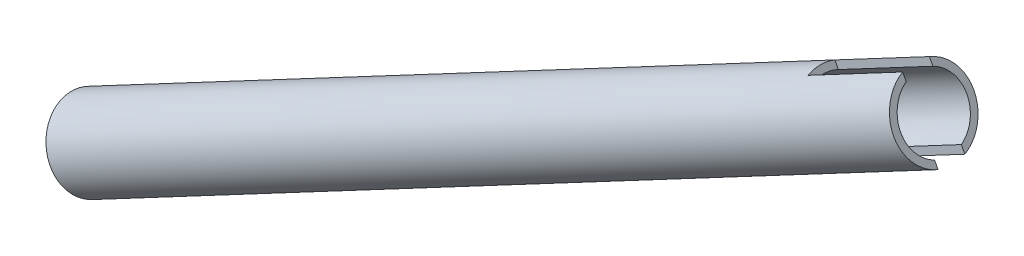
SolidWorks part; units mm, degrees
ref_plane "Front" through (0, 0, 0) normal (0, 0, 1) x (1, 0, 0)
ref_plane "Top" through (0, 0, 0) normal (0, 1, 0) x (1, 0, 0)
ref_plane "Right" through (0, 0, 0) normal (1, 0, 0) x (0, 0, -1)
sketch "Sketch1" plane through (0, 0, 0) normal (0, 0, 1) x (1, 0, 0)
  line L0 (375.7874, -136.2898) -> (576.0142, -30.0522)
  line L1 (328.6246, -152.4) -> (628.4169, 6.6657) construction
  line L2 (576.0142, -30.0522) -> (576.788, -31.5106)
  line L3 (576.788, -31.5106) -> (376.5613, -137.7482)
  line L4 (376.5613, -137.7482) -> (375.7874, -136.2898)
  line L6 (553.1437, -33.2732) -> (576.2246, -21.0268) construction
  dimension "D1" = 1.651
  dimension "D2" = 9.525
revolve "Revolve1" add sketch "Sketch1" angle 360 about L6
sketch "Sketch2" plane through (0, 0, 0) normal (0, 0, 1) x (1, 0, 0)
  line L0 (545.422, -26.5876) -> (554.3507, -43.4156)
  line L1 (554.3507, -43.4156) -> (576.788, -31.5106)
  line L2 (576.788, -31.5106) -> (567.8593, -14.6826)
  line L3 (567.8593, -14.6826) -> (545.422, -26.5876)
  line L4 (567.8593, -14.6826) -> (367.6326, -120.9202) construction
  line L5 (376.5613, -137.7482) -> (576.788, -31.5106) construction
  line L6 (576.0142, -30.0522) -> (568.6331, -16.1411) construction
  line L7 (547.2673, -30.0654) -> (544.291, -24.456) construction
extrude "Cut-Extrude1" cut sketch "Sketch2" along normal up to surface and the other way up to surface
move or copy body "Body-Move/Copy1" [suppressed] bodies to move or copy 102
equation "\"D1@Sketch1\"=\"a arm tube thickness@FS2-SU-RS-A-0002-V1, REAR LEFT SUSPENSION.Assembly\""
equation "\"D2@Sketch1\"=\"a arm tube diameter@FS2-SU-RS-A-0002-V1, REAR LEFT SUSPENSION.Assembly\"/2"
